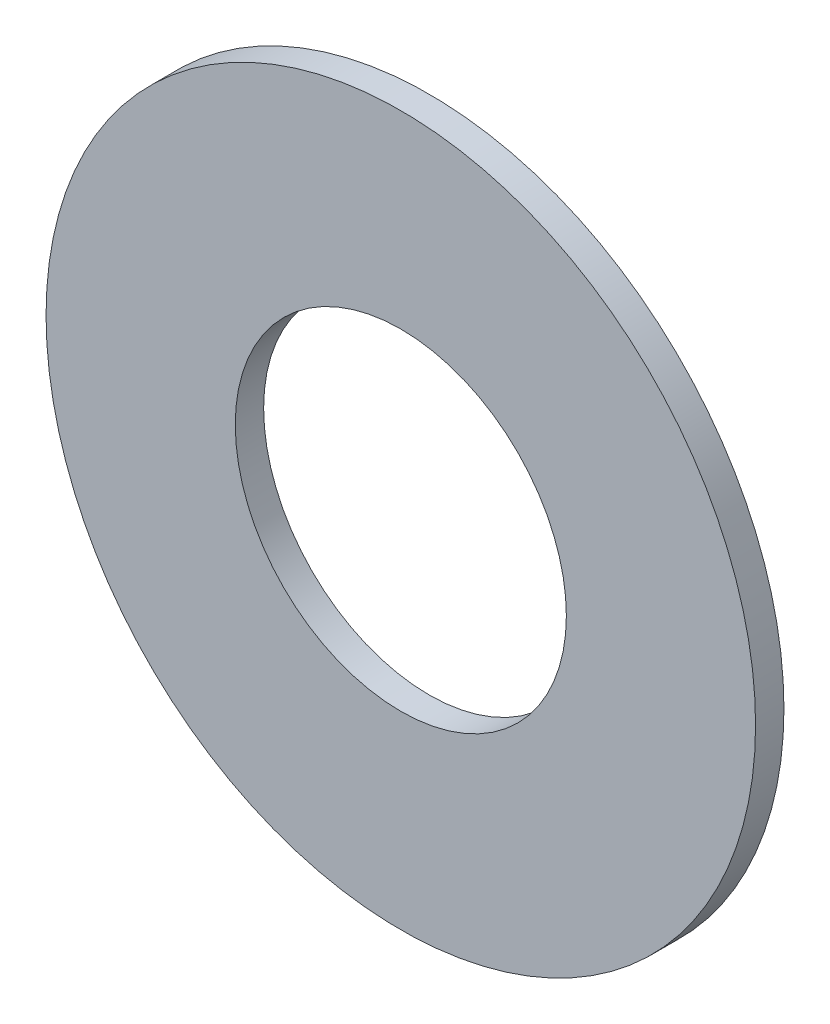
SolidWorks part; units mm, degrees
ref_plane "Front Plane" through (0, 0, 0) normal (0, 0, 1) x (1, 0, 0)
ref_plane "Top Plane" through (0, 0, 0) normal (0, 1, 0) x (1, 0, 0)
ref_plane "Right Plane" through (0, 0, 0) normal (1, 0, 0) x (0, 0, -1)
sketch "Sketch1" plane through (0, 0, 0) normal (0, 0, 1) x (1, 0, 0)
  circle A0 centre (0, 0) radius 17.5
  circle A1 centre (0, 0) radius 37.5
  dimension "D1" = 35
  dimension "D2" = 75
extrude "Boss-Extrude1" add sketch "Sketch1" along normal blind 3
